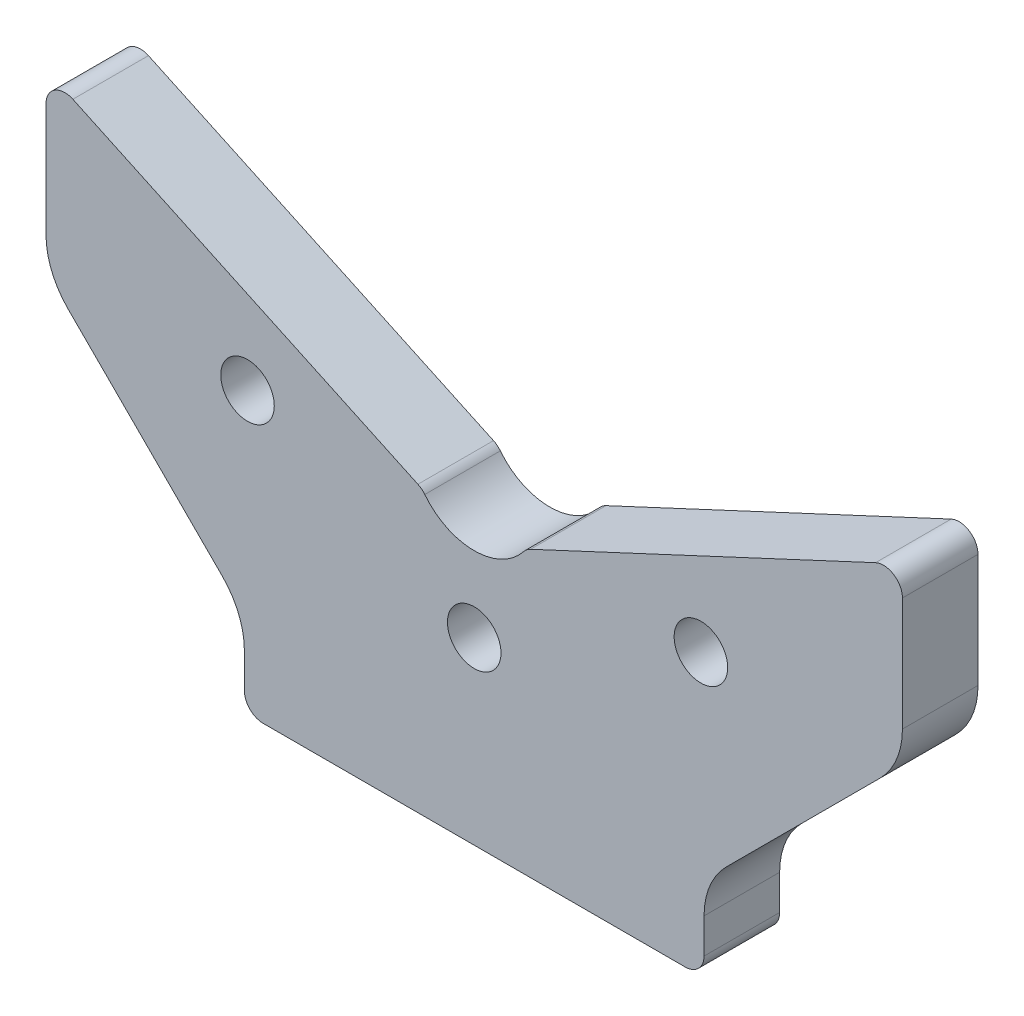
SolidWorks part; units mm, degrees
ref_plane "Front" through (0, 0, 0) normal (0, 0, 1) x (1, 0, 0)
ref_plane "Top" through (0, 0, 0) normal (0, 1, 0) x (1, 0, 0)
ref_plane "Right" through (0, 0, 0) normal (1, 0, 0) x (0, 0, -1)
sketch "Sketch1" plane through (0, 0, 0) normal (0, 0, 1) x (1, 0, 0)
  line L0 (36.5, 3) -> (36.5, 8.5294)
  line L1 (-36.5, 3) -> (-36.5, 8.5294)
  line L2 (0, 0) -> (33.5, 0)
  line L3 (0, 0) -> (-33.5, 0)
  line L4 (63.7321, 70.7189) -> (8.9396, 45.1687)
  line L5 (0, 0) -> (0, 41.0001) construction
  line L6 (-68, 49.9706) -> (-68, 68)
  line L7 (-63.7321, 70.7189) -> (-8.9396, 45.1687)
  line L8 (40.0147, 17.0147) -> (64.4853, 41.4853)
  line L10 (68, 49.9706) -> (68, 68)
  line L11 (-40.0147, 17.0147) -> (-64.4853, 41.4853)
  arc A0 (36.5, 8.5294) -> (40.0147, 17.0147) centre (48.5, 8.5294) cw
  arc A1 (-36.5, 8.5294) -> (-40.0147, 17.0147) centre (-48.5, 8.5294) ccw
  arc A2 (33.5, 0) -> (36.5, 3) centre (33.5, 3) ccw
  arc A3 (63.7321, 70.7189) -> (68, 68) centre (65, 68) cw
  arc A4 (-68, 68) -> (-63.7321, 70.7189) centre (-65, 68) cw
  arc A5 (64.4853, 41.4853) -> (68, 49.9706) centre (56, 49.9706) ccw
  arc A6 (-36.5, 3) -> (-33.5, 0) centre (-33.5, 3) ccw
  arc A9 (-64.4853, 41.4853) -> (-68, 49.9706) centre (-56, 49.9706) cw
  arc A10 (-7.8519, 44.3076) -> (7.8519, 44.3076) centre (0, 50.5001) ccw
  arc A11 (-7.8519, 44.3076) -> (-8.9396, 45.1687) centre (-10.2075, 42.4498) ccw
  arc A12 (7.8519, 44.3076) -> (8.9396, 45.1687) centre (10.2075, 42.4498) cw
  point P8 (36.5, 13.5)
  point P11 (-36.5, 13.5)
  point P15 (36.5, 0)
  point P19 (68, 72.7091)
  point P23 (-68, 72.7091)
  point P26 (68, 0)
  point P30 (-36.5, 0)
  point P32 (68, 45)
  point P43 (0, 41.0001)
  dimension "D5" = 26
  dimension "D6" = 3
  dimension "D7" = 12
  dimension "D8" = 3
  dimension "D13" = 12
  dimension "D15" = 10
  dimension "D16" = 3
  dimension "D2" = 73
  dimension "D3" = 65
  dimension "D4" = 25
  dimension "D9" = 136
  dimension "D10" = 71
  dimension "D11" = 45
  dimension "D14" = 9.5
extrude "Extrude1" add sketch "Sketch1" along normal blind 12
hole_wizard "M10 gevindhuller" positions "Sketch5" profile "Sketch4" legacy
sketch "Sketch5" plane through (0, 0, 12) normal (0, 0, 1) x (1, 0, 0)
  line L0 (0, 0) -> (0, 50.5001) construction
  line L1 (63.7321, 70.7189) -> (8.9396, 45.1687) construction
  point P6 (-36, 44.5467)
  point P10 (0, 28.5467)
  point P11 (36, 44.5467)
  dimension "D1" = 72
  dimension "D2" = 12
  dimension "D3" = 16
sketch "Sketch4" plane through (-36, 44.5467, 12) normal (1, 0, 0) x (0, -1, 0)
  line L0 (0, 0) -> (0, 24.5537)
  line L1 (0, 24.5537) -> (4.25, 22)
  line L2 (4.25, 22) -> (4.25, 0)
  line L4 (4.25, 0) -> (0, 0)
  line L6 (0, 24.5537) -> (-4.25, 22) construction
  line L7 (0, -4.2442) -> (0, 117.3081) construction
  dimension "Diameter" = 8.5
  dimension "Depth" = 22
  dimension "Drill Angle" = 118
cosmetic thread "Cosmetic Thread2" parameters "D1"=17, "D2"=10
cosmetic thread "Cosmetic Thread3" parameters "D1"=17, "D2"=10
cosmetic thread "Cosmetic Thread4" parameters "D1"=17, "D2"=10
